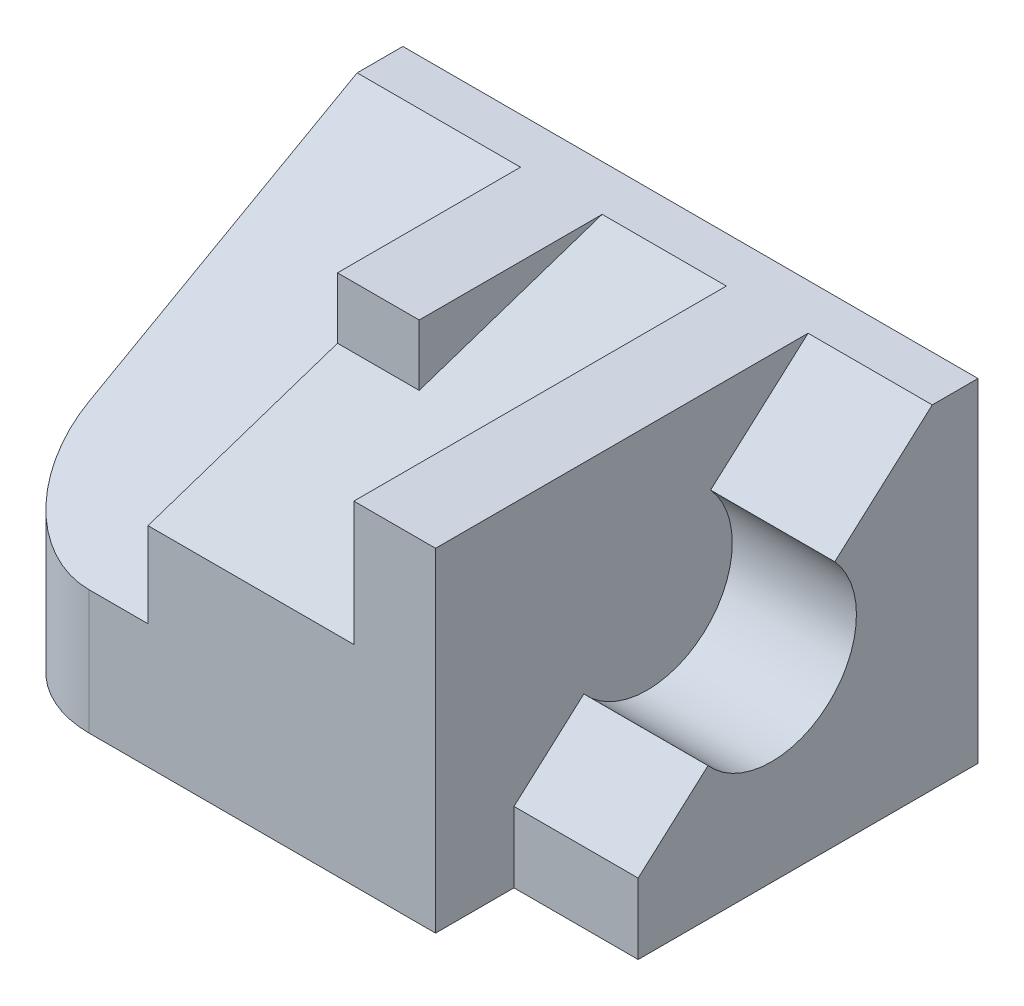
SolidWorks part; units mm, degrees
ref_plane "Front Plane" through (0, 0, 0) normal (0, 0, 1) x (1, 0, 0)
ref_plane "Top Plane" through (0, 0, 0) normal (0, 1, 0) x (1, 0, 0)
ref_plane "Right Plane" through (0, 0, 0) normal (1, 0, 0) x (0, 0, -1)
sketch "Sketch1" plane through (0, 0, 0) normal (0, 1, 0) x (1, 0, 0)
  line L0 (0, 0) -> (44, 0)
  line L1 (44, 0) -> (44, -26)
  line L2 (44, -26) -> (34.5, -26)
  line L3 (34.5, -26) -> (34.5, -32)
  line L4 (34.5, -32) -> (0, -32)
  line L5 (0, -32) -> (0, 0)
  dimension "D1" = 44
  dimension "D2" = 32
  dimension "D3" = 26
  dimension "D4" = 9.5
extrude "Boss-Extrude1" add sketch "Sketch1" along normal blind 25.5
sketch "Sketch2" plane through (0, 25.5, 0) normal (0, 1, 0) x (1, 0, 0)
  line L0 (44, -3.5) -> (34.5, -3.5)
  line L1 (34.5, -3.5) -> (34.5, -26)
  line L2 (28.25, -32) -> (28.25, -3.5)
  line L3 (28.25, -3.5) -> (18.75, -3.5)
  line L4 (18.75, -3.5) -> (18.75, -17.5)
  line L5 (18.75, -17.5) -> (12.5, -17.5)
  line L6 (0, 0) -> (0, -32)
  line L7 (0, -32) -> (34.5, -32)
  line L8 (34.5, -32) -> (34.5, -26)
  line L9 (34.5, -26) -> (44, -26)
  line L10 (44, -26) -> (44, 0)
  line L11 (44, 0) -> (0, 0)
  line L12 (0, 0) -> (0, -32)
  line L13 (0, -32) -> (34.5, -32)
  line L14 (34.5, -32) -> (34.5, -26)
  line L15 (34.5, -26) -> (44, -26)
  line L16 (44, -26) -> (44, 0)
  line L17 (44, 0) -> (0, 0)
  line L18 (12.5, -17.5) -> (12.5, -3.5)
  line L19 (12.5, -3.5) -> (0, -3.5)
  line L20 (12.5, -17.5) -> (12.5, -32)
  line L21 (12.5, -3.5) -> (18.75, -3.5)
  dimension "D2" = 6.25
  dimension "D3" = 3.5
  dimension "D4" = 12.5
  dimension "D5" = 17.5
  dimension "D6" = 9.5
  dimension "D1" = 0
sketch "Sketch3" plane through (0, 0, 0) normal (-1, 0, 0) x (0, 0, 1)
  line L0 (3.5, 25.5) -> (32, 9.5)
  line L4 (0, 0) -> (32, 0)
  line L5 (32, 0) -> (32, 25.5)
  line L6 (32, 25.5) -> (0, 25.5)
  line L7 (0, 25.5) -> (0, 0)
  line L8 (0, 0) -> (32, 0)
  line L9 (32, 0) -> (32, 25.5)
  line L10 (32, 25.5) -> (0, 25.5)
  line L11 (0, 25.5) -> (0, 0)
  point P2 (3.5, 25.5)
  line M6 (32, 0) -> (32, 25.5)
  line M7 (32, 25.5) -> (0, 25.5)
  dimension "D2" = 9.5
  dimension "D1" = 0
extrude "Cut-Extrude1" cut sketch "Sketch3" against normal blind 12.5 contours L0 M7 M6
sketch "Sketch4" plane through (12.5, 0, 0) normal (-1, 0, 0) x (0, 0, 1)
  line L0 (3.5, 25.5) -> (32, 16)
  line L1 (0, 0) -> (32, 0) construction
  line L3 (32, 25.5) -> (3.5, 25.5)
  line L4 (3.5, 25.5) -> (32, 9.5)
  line L5 (32, 9.5) -> (32, 25.5)
  line L6 (32, 25.5) -> (3.5, 25.5)
  line L7 (3.5, 25.5) -> (32, 9.5)
  line L8 (32, 9.5) -> (32, 25.5)
  line M1 (32, 25.5) -> (3.5, 25.5)
  line M3 (32, 9.5) -> (32, 25.5)
  dimension "D2" = 16
  dimension "D1" = 0
extrude "Cut-Extrude2" cut sketch "Sketch4" against normal blind 15.75 contours L0 M1 M3
extrude "Boss-Extrude2" add sketch "Sketch2" against normal up to surface contours L21 L18 L5 L4 up to face at (20.375, 20.75, 17.75)
sketch "Sketch5" plane through (44, 0, 0) normal (1, 0, 0) x (0, 0, -1)
  line L0 (0, 25.5) -> (-3.5, 25.5) construction
  line L1 (0, 25.5) -> (-3.5, 25.5)
  line L2 (-3.5, 25.5) -> (-26, 5.4)
  line L4 (-26, 0) -> (0, 0)
  line L5 (0, 0) -> (0, 25.5)
  line L6 (0, 25.5) -> (-26, 25.5)
  line L7 (-26, 25.5) -> (-26, 0)
  line L8 (-26, 0) -> (0, 0)
  line L9 (0, 0) -> (0, 25.5)
  line L10 (0, 25.5) -> (-26, 25.5)
  line L11 (-26, 25.5) -> (-26, 0)
  circle A0 centre (-15.8, 14.5) radius 6.5
  point P10 (-0.6378, 10.9443)
  line M7 (0, 25.5) -> (-26, 25.5)
  line M8 (-26, 25.5) -> (-26, 0)
  dimension "D3" = 13
  dimension "D2" = 5.4
  dimension "D4" = 11
  dimension "D5" = 15.8
  dimension "D1" = 0
extrude "Cut-Extrude3" cut sketch "Sketch5" against normal blind 9.5 contours L2 M7 M8 | A0
fillet "Fillet1" radius 8 1 edges at (0, 4.75, 32)
